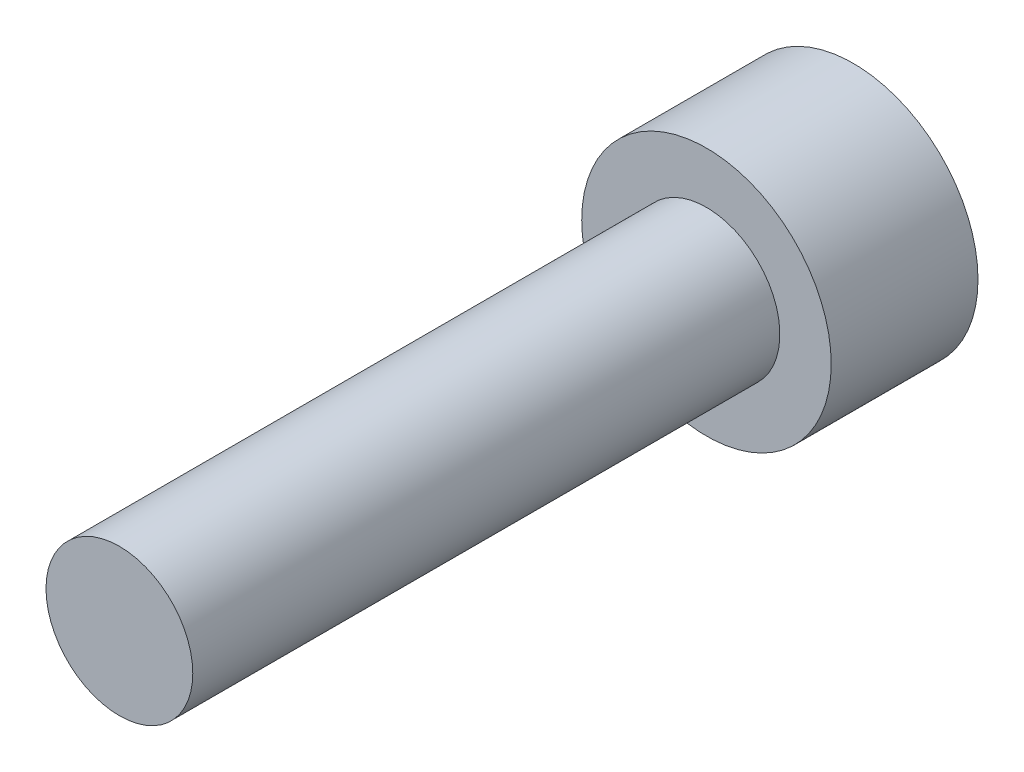
SolidWorks part; units mm, degrees
ref_plane "Alzado" through (0, 0, 0) normal (0, 0, 1) x (1, 0, 0)
ref_plane "Planta" through (0, 0, 0) normal (0, 1, 0) x (1, 0, 0)
ref_plane "Vista lateral" through (0, 0, 0) normal (1, 0, 0) x (0, 0, -1)
sketch "Croquis1" plane through (0, 0, 0) normal (0, 0, 1) x (1, 0, 0)
  circle A0 centre (0, 0) radius 2.5
  dimension "D1" = 5
extrude "Saliente-Extruir1" add sketch "Croquis1" along normal blind 20
sketch "Croquis2" plane through (0, 0, 0) normal (0, 0, -1) x (-1, 0, 0)
  circle A0 centre (0, 0) radius 4.25
  dimension "D1" = 8.5
extrude "Saliente-Extruir2" add sketch "Croquis2" along normal blind 5
sketch "Croquis3" plane through (0, 0, -5) normal (0, 0, -1) x (-1, 0, 0)
  line L1 (1.2675, 1.9305) -> (-1.0381, 2.0629)
  line L2 (-1.0381, 2.0629) -> (-2.3056, 0.1324)
  line L3 (-2.3056, 0.1324) -> (-1.2675, -1.9305)
  line L4 (-1.2675, -1.9305) -> (1.0381, -2.0629)
  line L5 (1.0381, -2.0629) -> (2.3056, -0.1324)
  line L6 (2.3056, -0.1324) -> (1.2675, 1.9305)
  circle A0 centre (0, 0) radius 2 construction
  dimension "D1" = 4
extrude "Cortar-Extruir1" cut sketch "Croquis3" against normal blind 2.5
